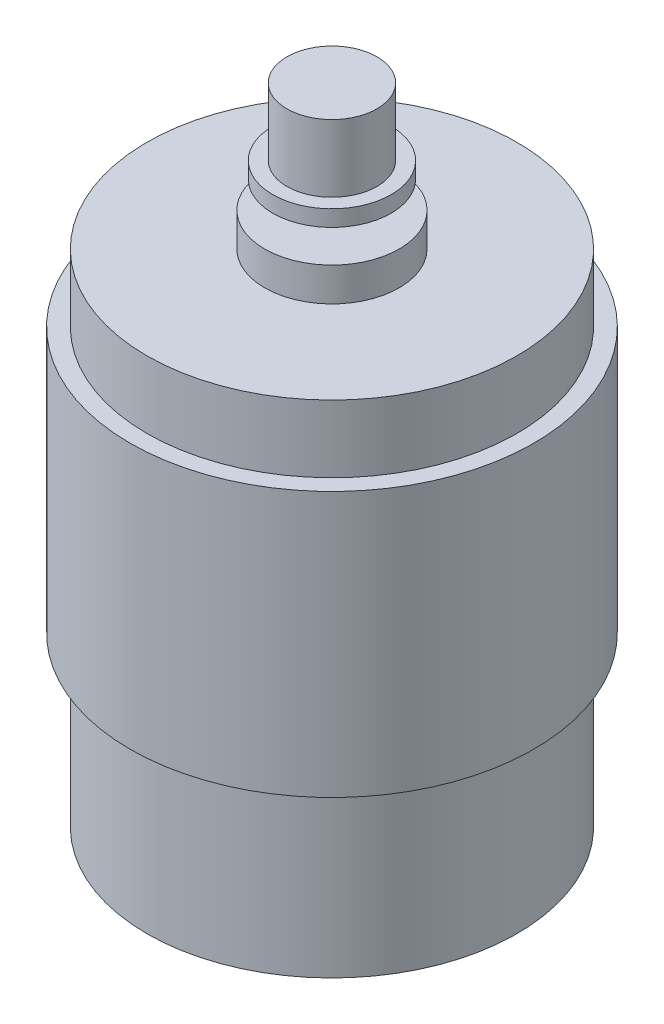
SolidWorks part; units mm, degrees
ref_plane "Alzado" through (0, 0, 0) normal (0, 0, 1) x (1, 0, 0)
ref_plane "Planta" through (0, 0, 0) normal (0, 1, 0) x (1, 0, 0)
ref_plane "Vista lateral" through (0, 0, 0) normal (1, 0, 0) x (0, 0, -1)
sketch "Croquis1" plane through (0, 0, 0) normal (0, 1, 0) x (1, 0, 0)
  circle A4 centre (0, 0) radius 13.75
  dimension "D1" = 27.5
extrude "Saliente-Extruir1" add sketch "Croquis1" along normal blind 12.5
sketch "Croquis2" plane through (0, 12.5, 0) normal (0, 1, 0) x (1, 0, 0)
  circle A0 centre (0, 0) radius 15
  dimension "D1" = 30
extrude "Saliente-Extruir2" add sketch "Croquis2" along normal blind 19.7
sketch "Croquis3" plane through (0, 32.2, 0) normal (0, 1, 0) x (1, 0, 0)
  circle A0 centre (0, 0) radius 13.75
  dimension "D1" = 27.5
extrude "Saliente-Extruir3" add sketch "Croquis3" along normal blind 5
sketch "Croquis4" plane through (0, 37.2, 0) normal (0, 1, 0) x (1, 0, 0)
  circle A0 centre (0, 0) radius 5
  dimension "D1" = 10
extrude "Saliente-Extruir4" add sketch "Croquis4" along normal blind 2.5
sketch "Croquis5" plane through (0, 39.7, 0) normal (0, 1, 0) x (1, 0, 0)
  circle A0 centre (0, 0) radius 1.15
  dimension "D1" = 2.3
extrude "Saliente-Extruir5" add sketch "Croquis5" along normal blind 2
sketch "Croquis6" plane through (0, 41.7, 0) normal (0, 1, 0) x (1, 0, 0)
  circle A0 centre (0, 0) radius 4.4
  dimension "D1" = 8.8
extrude "Saliente-Extruir6" add sketch "Croquis6" along normal blind 1.2
sketch "Croquis7" plane through (0, 42.9, 0) normal (0, 1, 0) x (1, 0, 0)
  circle A0 centre (0, 0) radius 3.35
  dimension "D1" = 6.7
extrude "Saliente-Extruir7" add sketch "Croquis7" along normal blind 5
